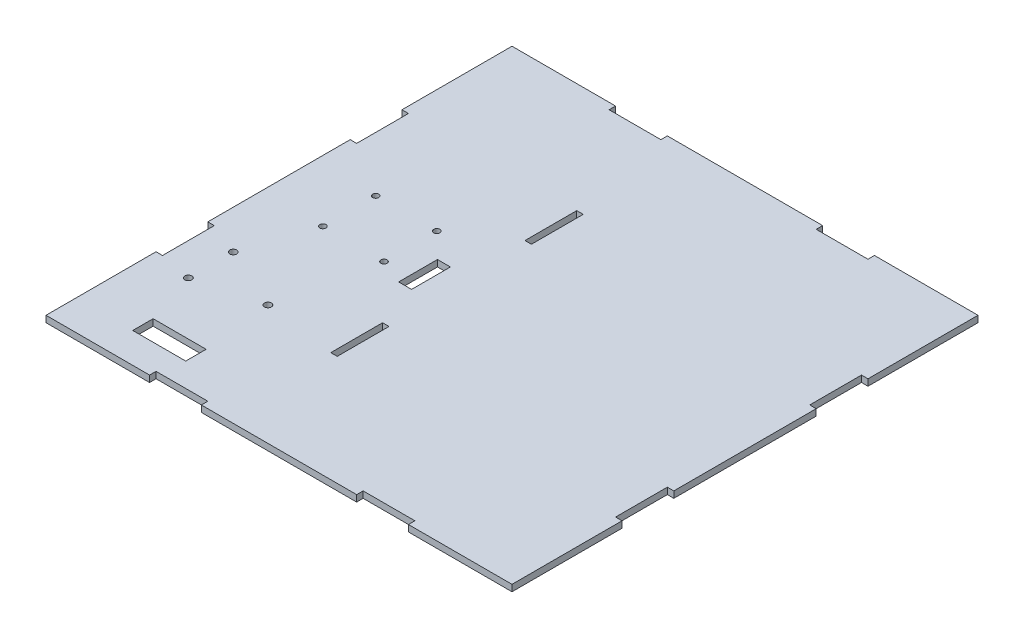
SolidWorks part; units mm, degrees
ref_plane "Front Plane" through (0, 0, 0) normal (0, 0, 1) x (1, 0, 0)
ref_plane "Top Plane" through (0, 0, 0) normal (0, 1, 0) x (1, 0, 0)
ref_plane "Right Plane" through (0, 0, 0) normal (1, 0, 0) x (0, 0, -1)
sketch "Sketch1" plane through (0, 0, 0) normal (0, 1, 0) x (1, 0, 0)
  line L1 (-114.3, 114.3) -> (114.3, 114.3)
  line L2 (-114.3, 114.3) -> (-114.3, -114.3)
  line L3 (-114.3, -114.3) -> (114.3, -114.3)
  line L4 (114.3, 114.3) -> (114.3, -114.3)
  dimension "D1" = 228.6
  dimension "D2" = 228.6
  dimension "D3" = 114.3
  dimension "D4" = 114.3
extrude "Boss-Extrude1" add sketch "Sketch1" along normal blind 3.175
sketch "Sketch2" plane through (0, 3.175, 0) normal (0, 1, 0) x (1, 0, 0)
  line L0 (-114.3, 114.3) -> (-114.3, -114.3) construction
  line L1 (-114.3, -114.3) -> (114.3, -114.3) construction
  line L3 (-86.5665, -89.4797) -> (-60.5665, -89.4797)
  line L4 (-86.5665, -89.4797) -> (-86.5665, -99.4797)
  line L5 (-86.5665, -99.4797) -> (-60.5665, -99.4797)
  line L6 (-60.5665, -89.4797) -> (-60.5665, -99.4797)
  line L7 (-41.9692, 5.4067) -> (-35.6192, 5.4067)
  line L8 (-41.9692, 5.4067) -> (-41.9692, -13.6433)
  line L9 (-41.9692, -13.6433) -> (-35.6192, -13.6433)
  line L10 (-35.6192, 5.4067) -> (-35.6192, -13.6433)
  circle A0 centre (-95.25, -63.5) radius 1.7145
  circle A1 centre (-95.25, -41.5) radius 1.7145
  circle A2 centre (-64.25, -55.5) radius 1.7145
  circle A3 centre (-84.1795, 17.3304) radius 1.5
  circle A4 centre (-54.2075, 17.3304) radius 1.5
  circle A5 centre (-54.2075, -8.5776) radius 1.5
  circle A6 centre (-84.1795, -8.5776) radius 1.5
  dimension "D1" = 22
  dimension "D6" = 2
  dimension "D2" = 8
  dimension "D3" = 31
  dimension "D4" = 19.05
  dimension "D5" = 50.8
  dimension "D8" = 26
  dimension "D9" = 10
  dimension "D10" = 6.35
  dimension "D11" = 19.05
  dimension "D7" = 2
extrude "Cut-Extrude1" cut sketch "Sketch2" against normal through all
sketch "Sketch3" plane through (0, 3.175, 0) normal (0, 1, 0) x (1, 0, 0)
  line L0 (-114.3, 114.3) -> (-114.3, -114.3) construction
  line L1 (-114.3, 60.325) -> (-111.125, 60.325)
  line L2 (-114.3, 60.325) -> (-114.3, 34.925)
  line L3 (-114.3, 34.925) -> (-111.125, 34.925)
  line L4 (-111.125, 60.325) -> (-111.125, 34.925)
  line L5 (114.3, -114.3) -> (114.3, 114.3) construction
  line L6 (-114.3, -34.925) -> (-111.125, -34.925)
  line L7 (-114.3, -34.925) -> (-114.3, -60.325)
  line L8 (-114.3, -60.325) -> (-111.125, -60.325)
  line L9 (-111.125, -34.925) -> (-111.125, -60.325)
  line L10 (114.3, 60.325) -> (111.125, 60.325)
  line L11 (114.3, 60.325) -> (114.3, 34.925)
  line L12 (114.3, 34.925) -> (111.125, 34.925)
  line L13 (111.125, 60.325) -> (111.125, 34.925)
  line L14 (-114.3, -114.3) -> (114.3, -114.3) construction
  line L15 (114.3, -34.925) -> (111.125, -34.925)
  line L16 (114.3, -34.925) -> (114.3, -60.325)
  line L17 (114.3, -60.325) -> (111.125, -60.325)
  line L18 (111.125, -34.925) -> (111.125, -60.325)
  line L19 (63.5, -114.3) -> (38.1, -114.3)
  line L20 (63.5, -114.3) -> (63.5, -111.125)
  line L21 (63.5, -111.125) -> (38.1, -111.125)
  line L22 (38.1, -114.3) -> (38.1, -111.125)
  line L23 (114.3, 114.3) -> (-114.3, 114.3) construction
  line L24 (-38.1, -114.3) -> (-63.5, -114.3)
  line L25 (-38.1, -114.3) -> (-38.1, -111.125)
  line L26 (-38.1, -111.125) -> (-63.5, -111.125)
  line L27 (-63.5, -114.3) -> (-63.5, -111.125)
  line L28 (-63.5, 114.3) -> (-38.1, 114.3)
  line L29 (-63.5, 114.3) -> (-63.5, 111.125)
  line L30 (-63.5, 111.125) -> (-38.1, 111.125)
  line L31 (-38.1, 114.3) -> (-38.1, 111.125)
  line L33 (38.1, 114.3) -> (63.5, 114.3)
  line L34 (38.1, 114.3) -> (38.1, 111.125)
  line L35 (38.1, 111.125) -> (63.5, 111.125)
  line L36 (63.5, 114.3) -> (63.5, 111.125)
  line L37 (-28.575, -34.925) -> (-25.4, -34.925)
  line L38 (-28.575, -34.925) -> (-28.575, -60.325)
  line L39 (-28.575, -60.325) -> (-25.4, -60.325)
  line L40 (-25.4, -34.925) -> (-25.4, -60.325)
  line L41 (-28.575, 60.325) -> (-25.4, 60.325)
  line L42 (-28.575, 60.325) -> (-28.575, 34.925)
  line L43 (-28.575, 34.925) -> (-25.4, 34.925)
  line L44 (-25.4, 60.325) -> (-25.4, 34.925)
  dimension "D1" = 3.175
  dimension "D2" = 3.175
  dimension "D3" = 3.175
  dimension "D4" = 3.175
  dimension "D5" = 3.175
  dimension "D6" = 3.175
  dimension "D7" = 3.175
  dimension "D8" = 3.175
  dimension "D9" = 25.4
  dimension "D10" = 25.4
  dimension "D11" = 25.4
  dimension "D12" = 25.4
  dimension "D13" = 25.4
  dimension "D14" = 25.4
  dimension "D15" = 25.4
  dimension "D16" = 25.4
  dimension "D17" = 50.8
  dimension "D18" = 50.8
  dimension "D19" = 50.8
  dimension "D20" = 50.8
  dimension "D21" = 53.975
  dimension "D22" = 53.975
  dimension "D23" = 53.975
  dimension "D24" = 53.975
  dimension "D25" = 3.175
  dimension "D26" = 3.175
  dimension "D27" = 25.4
  dimension "D28" = 25.4
  dimension "D29" = 88.9
  dimension "D30" = 88.9
extrude "Cut-Extrude2" cut sketch "Sketch3" against normal through all
